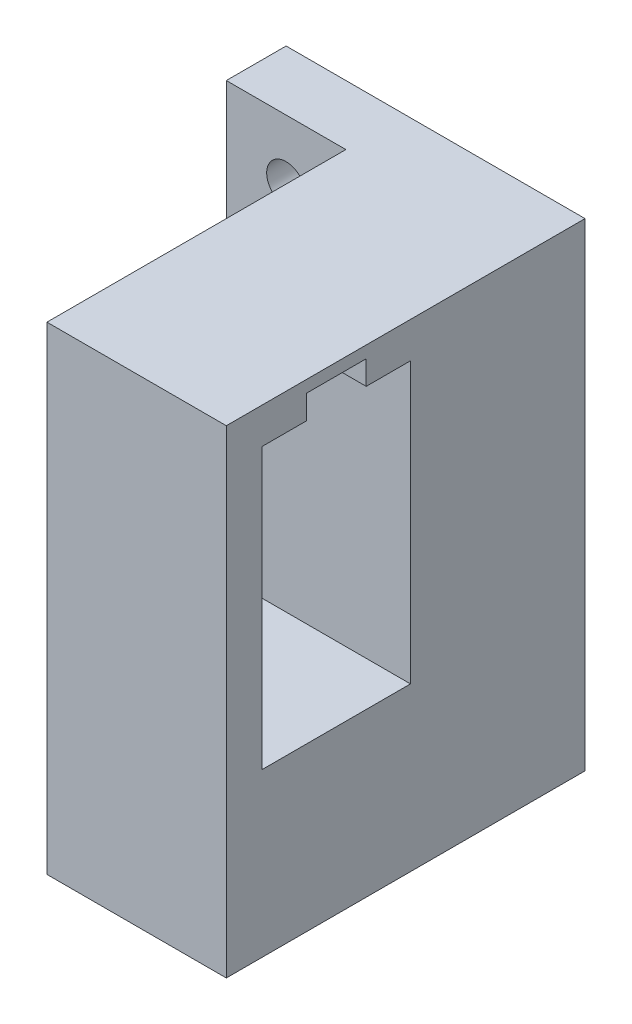
SolidWorks part; units mm, degrees
ref_plane "Plan de face" through (0, 0, 0) normal (0, 0, 1) x (1, 0, 0)
ref_plane "Plan de dessus" through (0, 0, 0) normal (0, 1, 0) x (1, 0, 0)
ref_plane "Plan de droite" through (0, 0, 0) normal (1, 0, 0) x (0, 0, -1)
sketch "Esquisse1" plane through (0, 0, 0) normal (0, 0, 1) x (1, 0, 0)
  line L1 (0, 0) -> (25, 0)
  line L2 (0, 0) -> (0, -40)
  line L3 (0, -40) -> (25, -40)
  line L4 (25, 0) -> (25, -40)
  dimension "D1" = 25
  dimension "D2" = 40
extrude "Boss.-Extru.1" add sketch "Esquisse1" along normal blind 5
sketch "Esquisse2" plane through (0, 0, 5) normal (0, 0, 1) x (1, 0, 0)
  line L0 (0, -40) -> (25, -40) construction
  line L1 (0, 0) -> (0, -40) construction
  circle A0 centre (5, -5) radius 1.625
  circle A1 centre (5, -35) radius 1.625
  dimension "D3" = 3.25
  dimension "D4" = 3.25
  dimension "D1" = 30
  dimension "D2" = 5
  dimension "D5" = 5
extrude "Enlèv. mat.-Extru.1" cut sketch "Esquisse2" against normal through all
sketch "Esquisse3" plane through (0, 0, 5) normal (0, 0, 1) x (1, 0, 0)
  line L0 (0, -40) -> (25, -40) construction
  line L1 (25, 0) -> (10, 0)
  line L2 (25, 0) -> (25, -40)
  line L3 (25, -40) -> (10, -40)
  line L4 (10, 0) -> (10, -40)
  dimension "D1" = 15
extrude "Boss.-Extru.2" add sketch "Esquisse3" along normal blind 25
sketch "Esquisse4" plane through (25, 0, 0) normal (1, 0, 0) x (0, 0, -1)
  line L0 (-30, -40) -> (-30, 0) construction
  line L1 (-14.6, -3) -> (-27, -3)
  line L2 (-14.6, -3) -> (-14.6, -26.4)
  line L3 (-14.6, -26.4) -> (-27, -26.4)
  line L4 (-27, -3) -> (-27, -26.4)
  line L9 (-30, 0) -> (0, 0) construction
  dimension "D1" = 3
  dimension "D2" = 3
  dimension "D5" = 23.4
  dimension "D6" = 12.4
extrude "Enlèv. mat.-Extru.2" cut sketch "Esquisse4" against normal blind 14 contours L1 L4 L3 L2
sketch "Esquisse5" plane through (25, 0, 0) normal (1, 0, 0) x (0, 0, -1)
  line L1 (-23.3, -1) -> (-18.3, -1)
  line L2 (-23.3, -1) -> (-23.3, -5)
  line L3 (-23.3, -5) -> (-18.3, -5)
  line L4 (-18.3, -1) -> (-18.3, -5)
  line L6 (-14.6, -3) -> (-27, -3) construction
  point P4 (-18.3, -3)
  dimension "D1" = 4
  dimension "D2" = 5
extrude "Enlèv. mat.-Extru.3" cut sketch "Esquisse5" against normal through all
